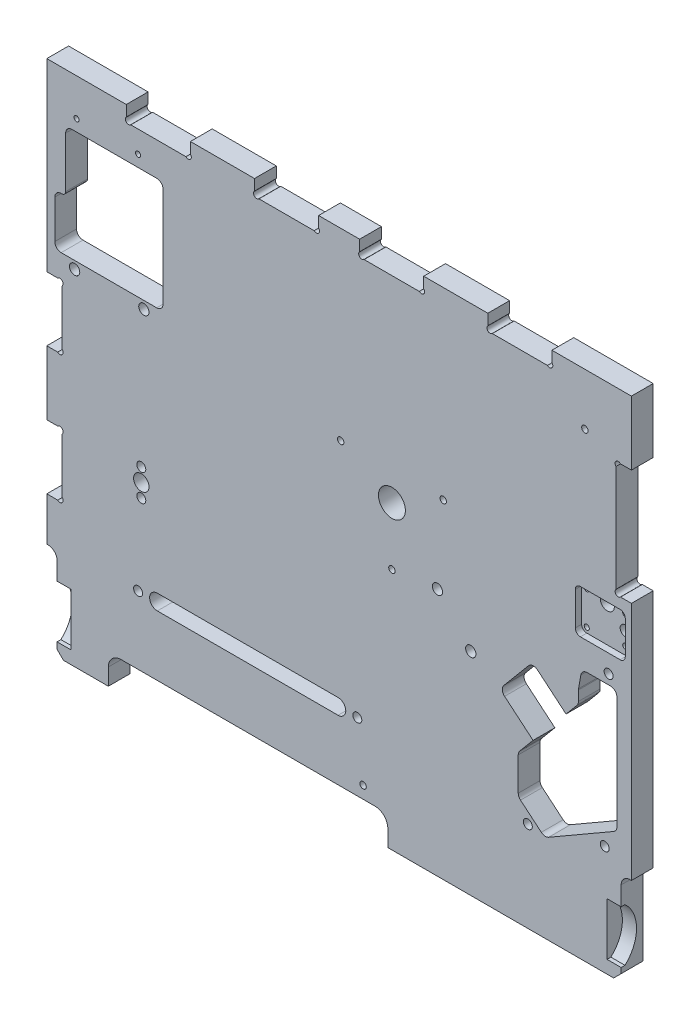
SolidWorks part; units mm, degrees
material "Pino"
ref_plane "Alzado" through (0, 0, 0) normal (0, 0, 1) x (1, 0, 0)
ref_plane "Planta" through (0, 0, 0) normal (0, 1, 0) x (1, 0, 0)
ref_plane "Vista lateral" through (0, 0, 0) normal (1, 0, 0) x (0, 0, -1)
sketch "Croquis1" plane through (0, 0, 0) normal (0, 0, 1) x (1, 0, 0)
  line L0 (-142.9016, -365.0897) -> (-1.9016, -365.0897) construction
  line L1 (-229.1084, -41.0897) -> (-167.1084, -41.0897)
  line L3 (-216.1084, -441.0897) -> (-181.1084, -441.0897)
  line L5 (-209.4016, -79.0897) -> (-143.4016, -79.0897)
  line L6 (-214.4016, -84.0897) -> (-214.4016, -123.5897)
  line L7 (-217.9016, -166.5897) -> (-143.4016, -166.5897)
  line L8 (-138.4016, -84.0897) -> (-138.4016, -161.5897)
  line L11 (-217.4016, -126.5897) -> (-217.9016, -126.5897)
  line L12 (-222.9016, -161.5897) -> (-222.9016, -131.5897)
  line L13 (-142.9016, -359.0897) -> (-1.9016, -359.0897)
  line L14 (-142.9016, -371.0897) -> (-1.9016, -371.0897)
  line L20 (215.5984, -250.0897) -> (215.5984, -337.7516)
  line L21 (213.0984, -342.0817) -> (162.3387, -371.3878)
  line L22 (156.6248, -370.8879) -> (140.4096, -357.2817)
  line L32 (138.6235, -353.4515) -> (138.6235, -327.6029)
  line L33 (139.7933, -324.389) -> (150.1937, -311.9942)
  line L34 (150.1937, -311.9942) -> (127.9784, -293.3534)
  line L35 (127.3621, -286.3092) -> (146.6458, -263.3279)
  line L36 (153.6899, -262.7116) -> (175.9052, -281.3525)
  line L37 (175.9052, -281.3525) -> (184.3772, -271.2559)
  line L39 (185.547, -268.0419) -> (185.547, -260.2992)
  line L40 (185.623, -259.431) -> (187.4232, -249.2214)
  line L41 (192.3472, -245.0897) -> (210.5984, -245.0897)
  line L42 (36.8916, -441.0897) -> (213.0567, -441.0897)
  line L44 (-181.1084, -441.0897) -> (-181.1084, -428.0897)
  line L45 (-171.1084, -418.0897) -> (26.8916, -418.0897)
  line L46 (36.8916, -441.0897) -> (36.8916, -428.0897)
  line L51 (218.8916, -435.2548) -> (218.8916, -375.2548)
  line L55 (-221.1084, -436.0897) -> (-221.1084, -376.0897)
  line L56 (213.0567, -441.0897) -> (218.8916, -435.2548)
  line L57 (-221.1084, -436.0897) -> (-216.1084, -441.0897)
  line L58 (-229.1084, -41.0897) -> (-229.1084, -185.0897)
  line L59 (226.8916, -41.0897) -> (226.8916, -91.0897)
  line L61 (64.8916, -41.0897) -> (114.8916, -41.0897)
  line L62 (-167.1084, -41.0897) -> (-167.1084, -49.5897)
  line L63 (-117.1084, -41.0897) -> (-117.1084, -49.5897)
  line L64 (-67.1084, -41.0897) -> (-67.1084, -49.5897)
  line L65 (-167.1084, -49.5897) -> (-167.1084, -53.0897) construction
  line L66 (-17.1084, -41.0897) -> (-17.1084, -49.5897)
  line L68 (-117.1084, -41.0897) -> (-67.1084, -41.0897)
  line L69 (-67.1084, -41.0897) -> (-67.1084, -67.0598) construction
  line L70 (-17.1084, -41.0897) -> (-17.1084, -67.0598) construction
  line L71 (-167.1084, -41.0897) -> (-167.1084, -67.0598) construction
  line L72 (-117.1084, -41.0897) -> (-117.1084, -67.0598) construction
  line L73 (-167.1084, -53.0897) -> (-163.6084, -53.0897) construction
  line L74 (-17.1084, -41.0897) -> (14.8916, -41.0897)
  line L75 (-163.6084, -53.0897) -> (-120.6084, -53.0897)
  line L76 (-63.6084, -53.0897) -> (-20.6084, -53.0897)
  line L77 (164.8916, -49.5897) -> (164.8916, -41.0897)
  line L78 (114.8916, -49.5897) -> (114.8916, -41.0897)
  line L79 (64.8916, -49.5897) -> (64.8916, -41.0897)
  line L80 (14.8916, -49.5897) -> (14.8916, -41.0897)
  line L81 (18.3916, -53.0897) -> (61.3916, -53.0897)
  line L82 (118.3916, -53.0897) -> (161.3916, -53.0897)
  line L83 (164.8916, -41.0897) -> (226.8916, -41.0897)
  line L84 (226.8916, -91.0897) -> (218.3916, -91.0897)
  line L85 (164.8916, -53.0897) -> (164.8916, -36.0208) construction
  line L86 (114.8916, -53.0897) -> (114.8916, -36.0208) construction
  line L87 (64.8916, -53.0897) -> (64.8916, -36.0208) construction
  line L88 (14.8916, -53.0897) -> (14.8916, -36.0208) construction
  line L89 (214.8916, -94.5897) -> (214.8916, -177.5897)
  line L90 (218.3916, -181.0897) -> (226.8916, -181.0897)
  line L91 (226.8916, -181.0897) -> (226.8916, -368.3266)
  line L92 (-229.1084, -335.0897) -> (-220.6084, -335.0897)
  line L93 (-217.1084, -331.5897) -> (-217.1084, -288.5897)
  line L94 (-220.6084, -285.0897) -> (-229.1084, -285.0897)
  line L95 (-229.1084, -235.0897) -> (-220.6084, -235.0897)
  line L96 (-217.1084, -231.5897) -> (-217.1084, -188.5897)
  line L97 (40.0984, -206.5897) -> (175.0984, -206.5897) construction
  line L98 (-220.6084, -185.0897) -> (-229.1084, -185.0897)
  line L99 (-229.1084, -235.0897) -> (-229.1084, -285.0897)
  line L100 (-229.1084, -335.0897) -> (-229.1084, -369.1615)
  line L101 (218.0984, -189.5897) -> (187.0984, -189.5897) construction
  line L102 (183.0984, -193.5897) -> (183.0984, -219.5897) construction
  line L103 (187.0984, -223.5897) -> (218.0984, -223.5897) construction
  line L104 (222.0984, -193.5897) -> (222.0984, -219.5897) construction
  line L105 (203.0984, -195.0897) -> (203.0984, -189.5897) construction
  line L108 (-220.6084, -335.0897) -> (-217.1084, -335.0897) construction
  line L109 (-217.1084, -335.0897) -> (-217.1084, -331.5897) construction
  line L110 (-220.6084, -285.0897) -> (-217.1084, -285.0897) construction
  line L111 (-217.1084, -285.0897) -> (-217.1084, -288.5897) construction
  line L112 (-220.6084, -185.0897) -> (-217.1084, -185.0897) construction
  line L113 (-217.1084, -185.0897) -> (-217.1084, -188.5897) construction
  line L114 (-217.1084, -231.5897) -> (-217.1084, -235.0897) construction
  line L115 (-217.1084, -235.0897) -> (-220.6084, -235.0897) construction
  line L116 (-120.6084, -53.0897) -> (-117.1084, -53.0897) construction
  line L117 (-117.1084, -53.0897) -> (-117.1084, -49.5897) construction
  line L118 (-67.1084, -49.5897) -> (-67.1084, -53.0897) construction
  line L119 (-67.1084, -53.0897) -> (-63.6084, -53.0897) construction
  line L120 (-20.6084, -53.0897) -> (-17.1084, -53.0897) construction
  line L121 (-17.1084, -53.0897) -> (-17.1084, -49.5897) construction
  line L122 (14.8916, -49.5897) -> (14.8916, -53.0897) construction
  line L123 (14.8916, -53.0897) -> (18.3916, -53.0897) construction
  line L124 (61.3916, -53.0897) -> (64.8916, -53.0897) construction
  line L125 (64.8916, -53.0897) -> (64.8916, -49.5897) construction
  line L126 (114.8916, -53.0897) -> (114.8916, -49.5897) construction
  line L127 (114.8916, -53.0897) -> (118.3916, -53.0897) construction
  line L128 (161.3916, -53.0897) -> (164.8916, -53.0897) construction
  line L129 (164.8916, -53.0897) -> (164.8916, -49.5897) construction
  line L130 (218.3916, -91.0897) -> (214.8916, -91.0897) construction
  line L131 (214.8916, -91.0897) -> (214.8916, -94.5897) construction
  line L132 (214.8916, -177.5897) -> (214.8916, -181.0897) construction
  line L133 (214.8916, -181.0897) -> (218.3916, -181.0897) construction
  line L134 (-221.1084, -376.0897) -> (-229.1084, -376.0897) construction
  line L135 (-229.1084, -376.0897) -> (-229.1084, -369.1615) construction
  arc A0 (-217.9016, -126.5897) -> (-222.9016, -131.5897) centre (-217.9016, -131.5897) ccw
  arc A1 (-209.4016, -79.0897) -> (-214.4016, -84.0897) centre (-209.4016, -84.0897) ccw
  arc A2 (-143.4016, -79.0897) -> (-138.4016, -84.0897) centre (-143.4016, -84.0897) cw
  arc A3 (-143.4016, -166.5897) -> (-138.4016, -161.5897) centre (-143.4016, -161.5897) ccw
  arc A4 (-217.9016, -166.5897) -> (-222.9016, -161.5897) centre (-217.9016, -161.5897) cw
  arc A5 (-214.4016, -123.5897) -> (-217.4016, -126.5897) centre (-217.4016, -123.5897) cw
  circle A6 centre (-205.9016, -70.0897) radius 2
  circle A7 centre (-157.9016, -70.0897) radius 2
  circle A8 centre (-207.4016, -172.5897) radius 4
  circle A9 centre (-153.4016, -172.5897) radius 4
  circle A10 centre (190.5984, -81.5897) radius 2.5
  circle A11 centre (40.0984, -206.5897) radius 10.5
  circle A14 centre (0.0984, -184.5897) radius 2.5
  circle A16 centre (209.1273, -237.5897) radius 3.5
  circle A18 centre (206.0984, -355.5897) radius 3.5
  circle A19 centre (146.0984, -370.5897) radius 3.5
  circle A20 centre (-155.4016, -290.5897) radius 6
  circle A21 centre (-155.4016, -280.0897) radius 3.5
  circle A22 centre (-155.4016, -301.0897) radius 3.5
  circle A23 centre (-157.9016, -365.0897) radius 3.5
  arc A25 (-142.9016, -359.0897) -> (-142.9016, -371.0897) centre (-142.9016, -365.0897) ccw
  arc A26 (-1.9016, -371.0897) -> (-1.9016, -359.0897) centre (-1.9016, -365.0897) ccw
  circle A27 centre (13.0984, -365.0897) radius 3.5
  circle A32 centre (80.0984, -184.5897) radius 2.5
  circle A34 centre (40.0984, -251.5897) radius 2.5
  circle A35 centre (75.5984, -247.0897) radius 4
  circle A36 centre (101.5984, -276.0897) radius 4
  circle A37 centre (17.5984, -408.5897) radius 2.5
  circle A38 centre (203.0984, -195.0897) radius 5.5
  circle A39 centre (187.0984, -193.5897) radius 2
  circle A40 centre (217.0984, -195.5897) radius 2
  circle A41 centre (187.0984, -219.5897) radius 2
  circle A42 centre (217.0984, -217.5897) radius 2
  circle A43 centre (217.0984, -207.0635) radius 4
  arc A48 (215.5984, -337.7516) -> (213.0984, -342.0817) centre (210.5984, -337.7516) cw
  arc A49 (162.3387, -371.3878) -> (156.6248, -370.8879) centre (159.8387, -367.0577) cw
  arc A50 (140.4096, -357.2817) -> (138.6235, -353.4515) centre (143.6235, -353.4515) cw
  arc A51 (138.6235, -327.6029) -> (139.7933, -324.389) centre (143.6235, -327.6029) cw
  arc A52 (127.9784, -293.3534) -> (127.3621, -286.3092) centre (131.1923, -289.5232) cw
  arc A53 (146.6458, -263.3279) -> (153.6899, -262.7116) centre (150.476, -266.5418) cw
  arc A54 (184.3772, -271.2559) -> (185.547, -268.0419) centre (180.547, -268.0419) ccw
  arc A55 (185.547, -260.2992) -> (185.623, -259.431) centre (190.547, -260.2992) cw
  arc A56 (187.4232, -249.2214) -> (192.3472, -245.0897) centre (192.3472, -250.0897) cw
  arc A57 (210.5984, -245.0897) -> (215.5984, -250.0897) centre (210.5984, -250.0897) cw
  arc A58 (-181.1084, -428.0897) -> (-171.1084, -418.0897) centre (-171.1084, -428.0897) cw
  arc A59 (26.8916, -418.0897) -> (36.8916, -428.0897) centre (26.8916, -428.0897) cw
  arc A60 (226.8916, -368.3266) -> (218.8916, -375.2548) centre (225.8916, -375.2548) ccw
  arc A61 (-221.1084, -376.0897) -> (-229.1084, -369.1615) centre (-228.1084, -376.0897) ccw
  arc A77 (187.0984, -189.5897) -> (183.0984, -193.5897) centre (187.0984, -193.5897) ccw construction
  arc A78 (218.0984, -189.5897) -> (222.0984, -193.5897) centre (218.0984, -193.5897) cw construction
  arc A79 (222.0984, -219.5897) -> (218.0984, -223.5897) centre (218.0984, -219.5897) cw construction
  arc A80 (187.0984, -223.5897) -> (183.0984, -219.5897) centre (187.0984, -219.5897) cw construction
  arc A81 (-220.6084, -335.0897) -> (-217.1084, -331.5897) centre (-218.8584, -333.3397) ccw
  arc A82 (-220.6084, -285.0897) -> (-217.1084, -288.5897) centre (-218.8584, -286.8397) cw
  arc A83 (-220.6084, -235.0897) -> (-217.1084, -231.5897) centre (-218.8584, -233.3397) ccw
  arc A84 (-220.6084, -185.0897) -> (-217.1084, -188.5897) centre (-218.8584, -186.8397) cw
  arc A85 (-167.1084, -49.5897) -> (-163.6084, -53.0897) centre (-165.3584, -51.3397) ccw
  arc A86 (-120.6084, -53.0897) -> (-117.1084, -49.5897) centre (-118.8584, -51.3397) ccw
  arc A87 (-67.1084, -49.5897) -> (-63.6084, -53.0897) centre (-65.3584, -51.3397) ccw
  arc A88 (-20.6084, -53.0897) -> (-17.1084, -49.5897) centre (-18.8584, -51.3397) ccw
  arc A89 (18.3916, -53.0897) -> (14.8916, -49.5897) centre (16.6416, -51.3397) cw
  arc A90 (61.3916, -53.0897) -> (64.8916, -49.5897) centre (63.1416, -51.3397) ccw
  arc A91 (114.8916, -49.5897) -> (118.3916, -53.0897) centre (116.6416, -51.3397) ccw
  arc A92 (161.3916, -53.0897) -> (164.8916, -49.5897) centre (163.1416, -51.3397) ccw
  arc A93 (218.3916, -91.0897) -> (214.8916, -94.5897) centre (216.6416, -92.8397) ccw
  arc A94 (218.3916, -181.0897) -> (214.8916, -177.5897) centre (216.6416, -179.3397) cw
  point P12 (-222.9016, -126.5897)
  point P15 (-214.4016, -79.0897)
  point P18 (-138.4016, -79.0897)
  point P21 (-138.4016, -166.5897)
  point P24 (-222.9016, -166.5897)
  point P67 (-72.4016, -365.0897)
  point P107 (218.8916, -441.0897)
  point P109 (-221.1084, -441.0897)
  point P125 (215.5984, -340.6383)
  point P128 (159.3067, -373.1383)
  point P131 (138.6235, -355.783)
  point P134 (138.6235, -325.783)
  point P137 (124.1482, -290.1395)
  point P140 (149.8597, -259.4977)
  point P143 (185.547, -269.8618)
  point P146 (185.547, -259.8618)
  point P149 (188.1517, -245.0897)
  point P154 (-181.1084, -418.0897)
  point P157 (36.8916, -418.0897)
  point P164 (218.5984, -368.0903)
  point P167 (-221.4016, -368.0903)
  point P179 (-117.1084, -41.0897)
  point P180 (-117.1084, -67.0598)
  dimension "D6" = 5
  dimension "D9" = 3
  dimension "D10" = 4
  dimension "D11" = 4
  dimension "D12" = 8
  dimension "D13" = 8
  dimension "D20" = 48
  dimension "D22" = 5
  dimension "D25" = 12
  dimension "D26" = 7
  dimension "D27" = 7
  dimension "D36" = 7
  dimension "D37" = 7
  dimension "D40" = 0
  dimension "D45" = 50
  dimension "D48" = 21
  dimension "D65" = 7
  dimension "D66" = 7
  dimension "D71" = 7
  dimension "D75" = 5
  dimension "D76" = 5
  dimension "D77" = 5
  dimension "D84" = 8
  dimension "D85" = 8
  dimension "D90" = 5
  dimension "D99" = 11
  dimension "D102" = 8
  dimension "D103" = 4
  dimension "D104" = 4
  dimension "D105" = 4
  dimension "D106" = 4
  dimension "D107" = 6
  dimension "D109" = 5
  dimension "D114" = 35
  dimension "D115" = 5
  dimension "D116" = 10
  dimension "D117" = 7
  dimension "D14" = 6.9282
  dimension "D21" = 6.9282
  dimension "D24" = 90.5
  dimension "D32" = 30
  dimension "D42" = 85.5
  dimension "D68" = 50
  dimension "D69" = 2.4749
  dimension "D73" = 50
  dimension "D92" = 60
  dimension "D97" = 7
  dimension "D47" = 39
  dimension "D3" = 87.5
  dimension "D4" = 38
  dimension "D5" = 76
  dimension "D8" = 40
  dimension "D15" = 6
  dimension "D16" = 6
  dimension "D17" = 54
  dimension "D18" = 9
  dimension "D19" = 9
  dimension "D23" = 40.5
  dimension "D28" = 0
  dimension "D29" = 0
  dimension "D30" = 10.5
  dimension "D31" = 10.5
  dimension "D33" = 239
  dimension "D34" = 12
  dimension "D35" = 141
  dimension "D38" = 15
  dimension "D39" = 15
  dimension "D41" = 324
  dimension "D43" = 34
  dimension "D44" = 19
  dimension "D46" = 50
  dimension "D49" = 60
  dimension "D50" = 50
  dimension "D51" = 15
  dimension "D52" = 90
  dimension "D53" = 40
  dimension "D54" = 10
  dimension "D55" = 34
  dimension "D56" = 40
  dimension "D57" = 34
  dimension "D58" = 65
  dimension "D59" = 27
  dimension "D60" = 10
  dimension "D61" = 15
  dimension "D62" = 30
  dimension "D63" = 18
  dimension "D64" = 204
  dimension "D67" = 85.5
  dimension "D70" = 70.5
  dimension "D72" = 203.5
  dimension "D74" = 165.5
  dimension "D78" = 400
  dimension "D79" = 143.5
  dimension "D80" = 143.5
  dimension "D81" = 5.8349
  dimension "D82" = 12
  dimension "D83" = 210.5
  dimension "D86" = 8
  dimension "D87" = 235
  dimension "D88" = 206
  dimension "D89" = 8
  dimension "D91" = 32.5
  dimension "D93" = 218
  dimension "D94" = 23
  dimension "D95" = 73
  dimension "D96" = 60
  dimension "D98" = 73
  dimension "D100" = 4.7932
  dimension "D101" = 135
  dimension "D108" = 5
  dimension "D110" = 148.5
  dimension "D111" = 148.5
  dimension "D112" = 176.5
  dimension "D113" = 10.5262
  dimension "D118" = 40
  dimension "D119" = 152.5
  dimension "D122" = 26
  dimension "D123" = 34.0718
  dimension "D124" = 50
  dimension "D125" = 144
  dimension "D126" = 43
  dimension "D127" = 83
  dimension "D128" = 456
  dimension "D129" = 8.5
  dimension "D130" = 50
  dimension "D131" = 90
extrude "Saliente-Extruir1" add sketch "Croquis1" along normal blind 17
sketch "Croquis4" plane through (0, 0, 0) normal (0, 0, -1) x (-1, 0, 0)
  circle A0 centre (198.9016, -416.573) radius 7.5
  dimension "D1" = 15
sketch "Desbaste Ranura 2mm" plane through (0, 0, 0) normal (0, 0, 1) x (1, 0, 0)
  line L0 (-1.9016, -371.0897) -> (-3.0696, -371.0897)
  line L1 (-3.0696, -371.0897) -> (71.093, -422.0226)
  line L2 (74.5348, -423.1079) -> (86.5783, -422.9306)
  line L3 (85.6703, -410.9707) -> (76.4025, -411.0748)
  line L4 (76.4025, -411.0748) -> (19.0984, -370.9635)
  line L5 (19.0984, -370.9635) -> (19.0984, -364.0897)
  line L6 (7.0984, -364.0898) -> (4.0805, -364.5522)
  line L7 (85.6703, -410.9707) -> (127.5891, -399.0766)
  line L8 (127.5891, -399.0766) -> (122.7611, -371.0253)
  line L9 (135.2873, -368.8694) -> (140.8753, -401.3361)
  line L10 (134.2099, -409.0303) -> (86.5783, -422.9306)
  line L11 (13.0984, -374.0897) -> (13.0984, -364.0897) construction
  line L12 (7.0984, -370.0897) -> (7.0984, -364.0898) construction
  line L13 (13.0984, -374.0897) -> (74.5912, -416.9289) construction
  line L14 (74.5912, -416.9289) -> (86.5333, -416.9196) construction
  line L15 (86.5333, -416.9196) -> (134.3949, -402.4507) construction
  line L16 (134.3949, -402.4507) -> (129.0242, -369.9474) construction
  arc A1 (19.0984, -364.0897) -> (7.0984, -364.0898) centre (13.0984, -364.0897) ccw
  arc A2 (4.0805, -364.5522) -> (-1.9016, -371.0897) centre (-1.9016, -365.0839) cw
  arc A3 (74.5348, -423.1079) -> (71.093, -422.0226) centre (74.5912, -416.9289) cw
  arc A4 (135.2873, -368.8694) -> (122.7611, -371.0253) centre (129.0242, -369.9474) ccw
  arc A5 (134.2099, -409.0303) -> (140.8753, -401.3361) centre (131.5797, -400.0176) ccw
extrude "Cortar-Extruir8" cut sketch "Desbaste Ranura 2mm" along normal blind 2
sketch "Croquis8" plane through (0, 0, 0) normal (0, 0, 1) x (1, 0, 0)
  line L0 (-155.4016, -301.0897) -> (-170.7814, -301.0897) construction
  line L1 (-155.4016, -313.6503) -> (-155.4016, -265.7412) construction
  line L2 (-155.4016, -280.0897) -> (-170.7814, -280.0897) construction
  line L3 (-165.4016, -301.0897) -> (-165.4016, -280.0897)
  line L4 (-145.4016, -280.0897) -> (-145.4016, -301.0897)
  arc A2 (-145.4016, -280.0897) -> (-165.4016, -280.0897) centre (-155.4016, -280.0897) ccw
  arc A3 (-145.4016, -301.0897) -> (-165.4016, -301.0897) centre (-155.4016, -301.0897) cw
  point P12 (-155.4016, -289.6958)
  dimension "D1" = 10
  dimension "D2" = 10
extrude "Cortar-Extruir9" cut sketch "Croquis8" along normal blind 4
ref_plane "Visagra izq" through (-221.1084, 0, 0) normal (-1, 0, 0) x (0, 0, 1)
sketch "Vis Izq" plane through (-221.1084, 0, 0) normal (-1, 0, 0) x (0, 0, 1)
  line L0 (0, -390.0897) -> (17, -390.0897) construction
  line L1 (17, -436.0897) -> (17, -376.0897) construction
  line L2 (8.5, -390.0897) -> (8.5, -376.0897) construction
  line L3 (17, -376.0897) -> (0, -376.0897) construction
  line L4 (17, -390.0897) -> (14, -390.0897)
  line L5 (17, -390.0897) -> (17, -431.0897)
  line L6 (17, -435.2548) -> (17, -375.2548) construction
  line L7 (17, -431.0897) -> (14, -431.0897)
  line L8 (17, -410.5897) -> (5, -410.5897) construction
  arc A0 (14, -431.0897) -> (14, -390.0897) centre (32.8472, -410.5897) cw
  point P18 (5, -410.5897)
  dimension "D1" = 14
  dimension "D2" = 3
  dimension "D3" = 12
  dimension "D4" = 55
ref_plane "Visagra Der" through (218.8916, 0, 0) normal (1, 0, 0) x (0, 0, -1)
sketch "Vis Der" plane through (218.8916, 0, 0) normal (1, 0, 0) x (0, 0, -1)
  line L0 (-8.5, -376.0897) -> (-8.5, -390.0897) construction
  line L1 (0, -390.0897) -> (-17, -390.0897) construction
  line L5 (-17, -390.0897) -> (-17, -431.0897)
  line L6 (-17, -431.0897) -> (-14, -431.0897)
  line L7 (-17, -390.0897) -> (-14, -390.0897)
  arc A0 (-14, -431.0897) -> (-14, -390.0897) centre (-32.8472, -410.5897) ccw
ref_plane "Plano sobre base" through (0, 0, 0) normal (0, 0, -1) x (-1, 0, 0)
sketch "Cortar extruir 10" plane through (0, 0, 0) normal (0, 0, -1) x (-1, 0, 0)
  line L0 (198.9016, -416.573) -> (198.9016, -441.0897) construction
  line L2 (198.9016, -416.573) -> (221.1084, -416.573)
  line L3 (221.1084, -436.0897) -> (221.1084, -376.0897) construction
  circle A0 centre (198.9016, -416.573) radius 7.5
  dimension "D1" = 15
extrude "Cortar-Extruir10" cut sketch "Croquis4" against normal blind 12 contours A0
extrude "Cortar-Extruir11" cut sketch "Vis Der" against normal blind 11
extrude "Cortar-Extruir12" cut sketch "Vis Izq" against normal blind 11
ref_plane "Plano4" through (0, 0, 17) normal (0, 0, 1) x (1, 0, 0)
sketch "Base Brazo" plane through (0, 0, 17) normal (0, 0, 1) x (1, 0, 0)
  line L4 (175.0984, -206.5897) -> (40.0984, -206.5897) construction
  line L11 (222.0984, -186.5897) -> (178.0984, -186.5897) construction
  line L12 (175.0984, -206.5897) -> (175.0984, -189.5897) construction
  line L17 (223.8623, -226.5897) -> (178.0984, -226.5897) construction
  line L18 (175.0984, -223.5897) -> (175.0984, -206.5897) construction
  line L19 (226.0984, -221.5897) -> (226.0984, -187.5897) construction
  line L22 (222.0984, -219.5897) -> (222.0984, -193.5897)
  line L23 (218.0984, -189.5897) -> (187.0984, -189.5897)
  line L24 (183.0984, -193.5897) -> (183.0984, -219.5897)
  line L25 (187.0984, -223.5897) -> (218.0984, -223.5897)
  line L26 (226.8916, -181.0897) -> (226.8916, -368.3266) construction
  line L27 (164.8916, -41.0897) -> (226.8916, -41.0897) construction
  arc A8 (226.0984, -187.5897) -> (222.0984, -186.5897) centre (223.5698, -189.2041) ccw construction
  arc A9 (223.8623, -226.5897) -> (226.0984, -221.5897) centre (223.8623, -223.5897) ccw construction
  arc A10 (178.0984, -226.5897) -> (175.0984, -223.5897) centre (178.0984, -223.5897) cw construction
  arc A11 (175.0984, -189.5897) -> (178.0984, -186.5897) centre (178.0984, -189.5897) cw construction
  arc A12 (218.0984, -223.5897) -> (222.0984, -219.5897) centre (218.0984, -219.5897) ccw
  arc A13 (222.0984, -193.5897) -> (218.0984, -189.5897) centre (218.0984, -193.5897) ccw
  arc A14 (183.0984, -219.5897) -> (187.0984, -223.5897) centre (187.0984, -219.5897) ccw
  arc A15 (183.0984, -193.5897) -> (187.0984, -189.5897) centre (187.0984, -193.5897) cw
  point P8 (225.0984, -224.5897)
  point P12 (175.0984, -224.5897)
  dimension "D5" = 4
  dimension "D8" = 39
  dimension "D7" = 3
  dimension "D1" = 135
  dimension "D2" = 20
  dimension "D3" = 20
  dimension "D4" = 3
  dimension "D6" = 4
  dimension "D9" = 148.5
  dimension "D10" = 0.7932
extrude "Cortar-Extruir13" cut sketch "Base Brazo" against normal blind 5
